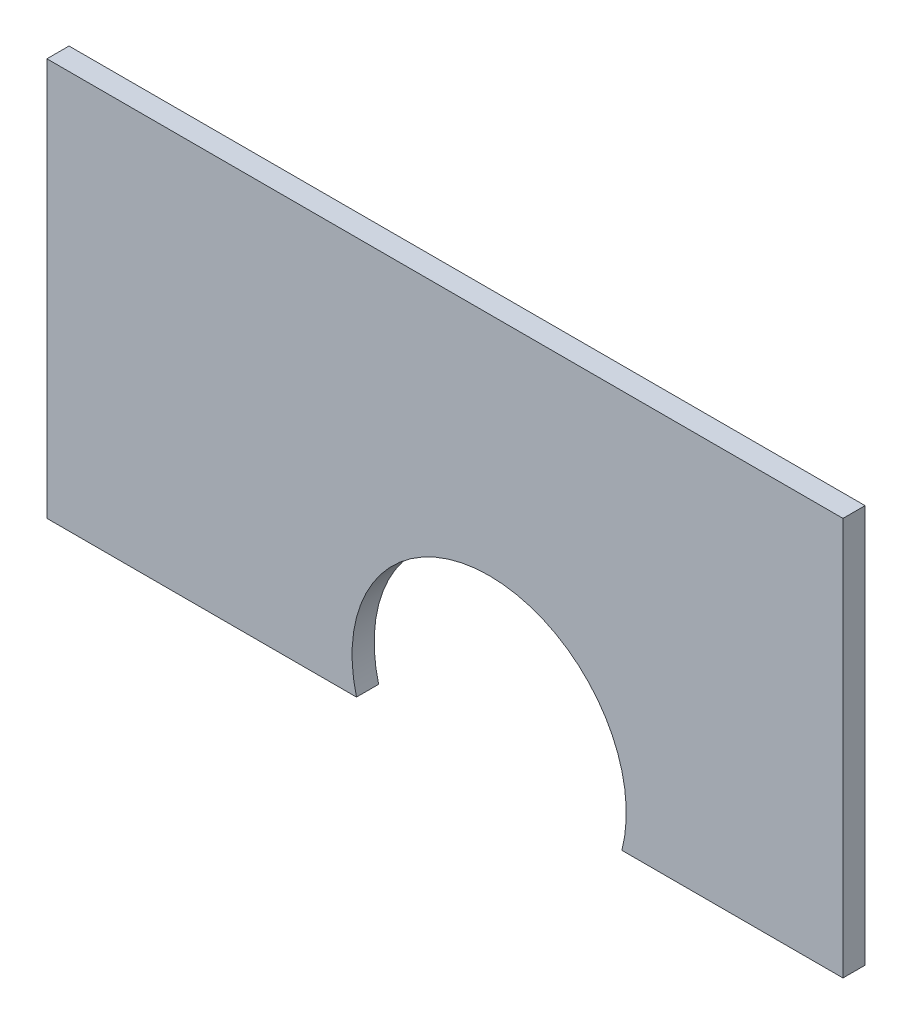
SolidWorks part; units mm, degrees
ref_plane "Front Plane" through (0, 0, 0) normal (0, 0, 1) x (1, 0, 0)
ref_plane "Top Plane" through (0, 0, 0) normal (0, 1, 0) x (1, 0, 0)
ref_plane "Right Plane" through (0, 0, 0) normal (1, 0, 0) x (0, 0, -1)
sketch "Sketch2" plane through (0, 0, 0) normal (0, 0, 1) x (1, 0, 0)
  line L6 (0, 164.3795) -> (0, -15.6205) construction
  line L7 (-200, 164.3795) -> (-200, -15.6205)
  line L10 (160, 164.3795) -> (160, -15.6205)
  line L12 (-60, -15.6205) -> (60, -15.6205) construction
  line L13 (-60, -15.6205) -> (-200, -15.6205)
  line L14 (60, -15.6205) -> (160, -15.6205)
  line L15 (-200, 164.3795) -> (160, 164.3795)
  arc A2 (60, -15.6205) -> (-60, -15.6205) centre (0, 0) ccw
  dimension "D1" = 62
  dimension "D3" = 200
  dimension "D4" = 120
  dimension "D2" = 160
  dimension "D5" = 180
extrude "Boss-Extrude1" add sketch "Sketch2" along normal blind 10
